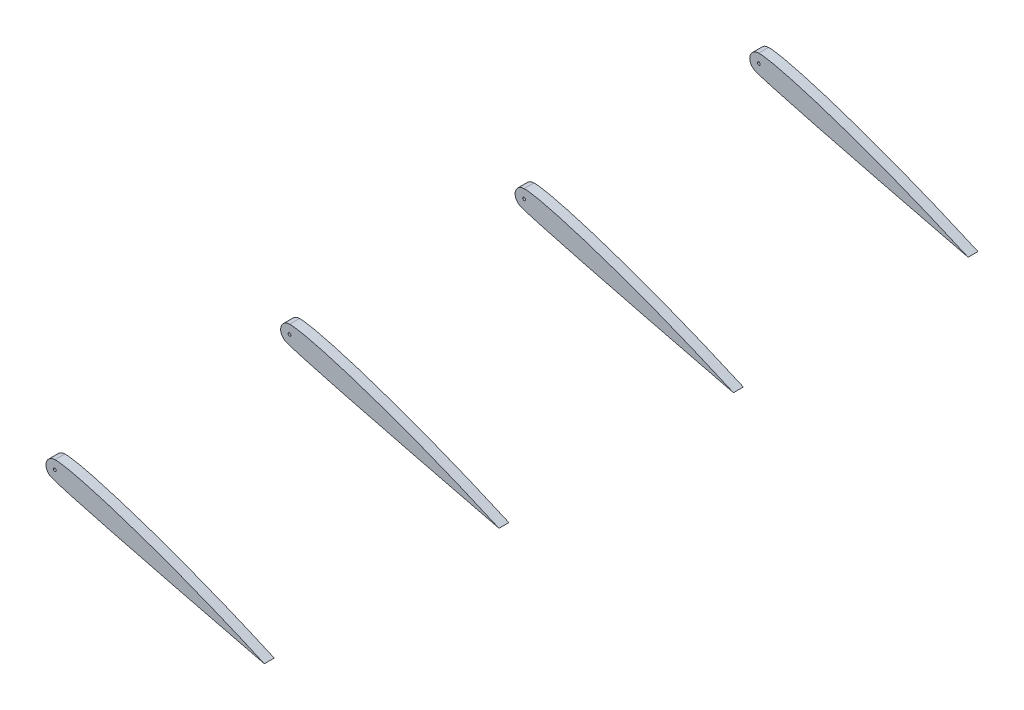
SolidWorks part; units mm, degrees
material "Balsa"
ref_plane "Front Plane" through (0, 0, 0) normal (0, 0, 1) x (1, 0, 0)
ref_plane "Top Plane" through (0, 0, 0) normal (0, 1, 0) x (1, 0, 0)
ref_plane "Right Plane" through (0, 0, 0) normal (1, 0, 0) x (0, 0, -1)
sketch "Sketch1" plane through (0, 0, 0) normal (0, 0, 1) x (1, 0, 0)
  arc A0 (-30.4045, 10.8094) -> (-31.8391, 5.8453) centre (-30.4045, 8.12) ccw
  spline S0 degree 3 poles (-30.4045, 10.8094) (-26.12, 11.2273) (0.623, 3.418) (33.0938, -11.0183) knots 0 0 0 0 1 1 1 1
  spline S1 degree 2 poles (-31.8391, 5.8453) (-29.6319, 4.2675) (33.0938, -11.0183) knots 0 0 0 1 1 1
extrude "Boss-Extrude1" add sketch "Sketch1" along normal blind 3 contours S0 S1 A0
ref_plane "Plane1" through (0, 0, -71.12) normal (0, 0, 1) x (1, 0, 0)
ref_plane "Plane2" through (0, 0, -142.24) normal (0, 0, 1) x (1, 0, 0)
ref_plane "Plane3" through (0, 0, -213.36) normal (0, 0, 1) x (1, 0, 0)
sketch "Sketch3" plane through (0, 0, -71.12) normal (0, 0, 1) x (1, 0, 0)
  arc A0 (-30.4045, 10.8094) -> (-31.8391, 5.8453) centre (-30.4045, 8.12) ccw
  spline S0 degree 3 poles (-30.4045, 10.8094) (-26.12, 11.2273) (0.623, 3.418) (33.0938, -11.0183) knots 0 0 0 0 1 1 1 1
  spline S1 degree 2 poles (-31.8391, 5.8453) (-29.6319, 4.2675) (33.0938, -11.0183) knots 0 0 0 1 1 1
extrude "Boss-Extrude2" add sketch "Sketch3" along normal blind 3 separate body
sketch "Sketch4" plane through (0, 0, -142.24) normal (0, 0, 1) x (1, 0, 0)
  arc A0 (-30.4605, 10.8118) -> (-31.8951, 5.8477) centre (-30.4605, 8.1224) ccw
  spline S0 degree 3 poles (-30.4605, 10.8118) (-26.176, 11.2297) (0.567, 3.4204) (33.0379, -11.0159) knots 0 0 0 0 1 1 1 1
  spline S1 degree 2 poles (-31.8951, 5.8477) (-29.6879, 4.2699) (33.0379, -11.0159) knots 0 0 0 1 1 1
extrude "Boss-Extrude3" add sketch "Sketch4" along normal blind 3 separate body
sketch "Sketch5" plane through (0, 0, -213.36) normal (0, 0, 1) x (1, 0, 0)
  arc A0 (-30.4605, 10.8118) -> (-31.8951, 5.8477) centre (-30.4605, 8.1224) ccw
  spline S0 degree 3 poles (-30.4605, 10.8118) (-26.176, 11.2297) (0.567, 3.4204) (33.0379, -11.0159) knots 0 0 0 0 1 1 1 1
  spline S1 degree 2 poles (-31.8951, 5.8477) (-29.6879, 4.2699) (33.0379, -11.0159) knots 0 0 0 1 1 1
extrude "Boss-Extrude4" add sketch "Sketch5" along normal blind 3 separate body
sketch "Sketch6" plane through (0, 0, 3) normal (0, 0, 1) x (1, 0, 0)
  circle A0 centre (-30.4045, 8.12) radius 0.4323
extrude "Cut-Extrude1" cut sketch "Sketch6" against normal through all
